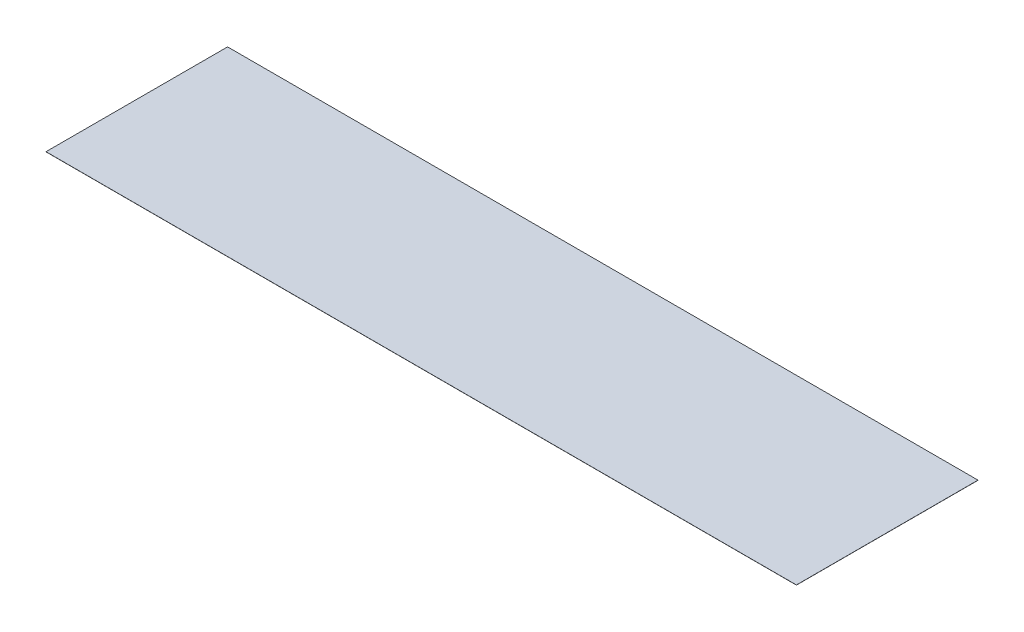
SolidWorks part; units mm, degrees
ref_plane "Front Plane" through (0, 0, 0) normal (0, 0, 1) x (1, 0, 0)
ref_plane "Top Plane" through (0, 0, 0) normal (0, 1, 0) x (1, 0, 0)
ref_plane "Right Plane" through (0, 0, 0) normal (1, 0, 0) x (0, 0, -1)
sketch "Sketch1" plane through (0, 0, 0) normal (0, 1, 0) x (1, 0, 0)
  line B0 (0, 1219.2) -> (5038.8608, 1219.2)
  line B1 (0, 1219.2) -> (0, 0)
  line B2 (0, 0) -> (5038.8608, 0)
  line B3 (5038.8608, 1219.2) -> (5038.8608, 0)
sketch_block_instance "table-1"
sketch_block "Block1"
extrude "Boss-Extrude1" add sketch "Sketch1" along normal blind 1
